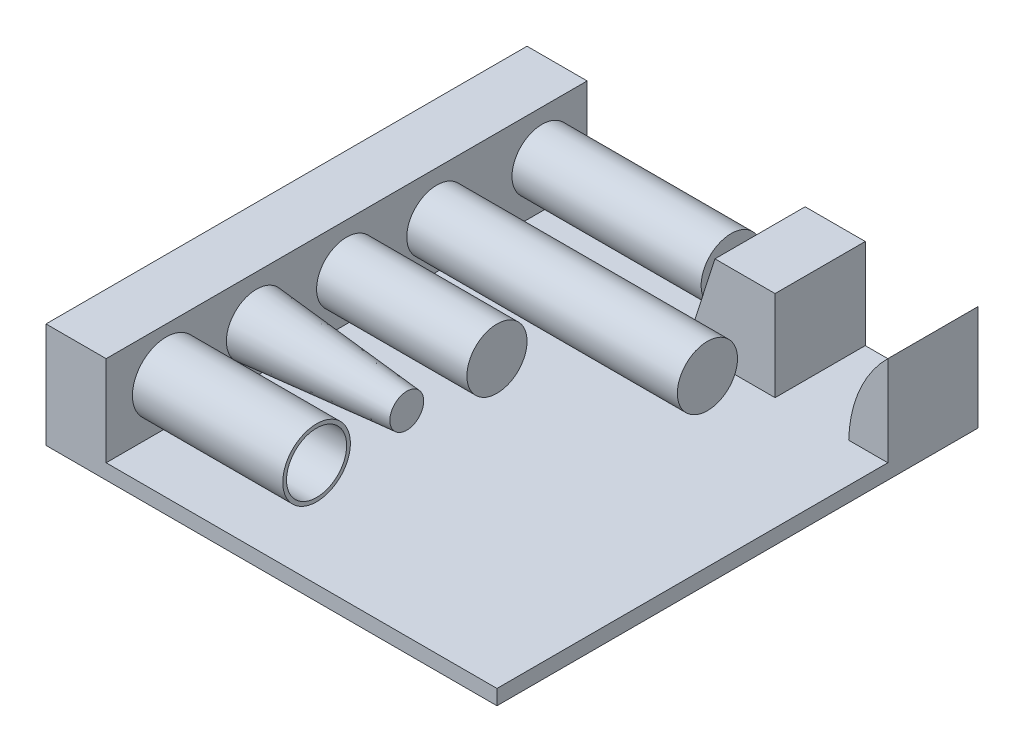
SolidWorks part; units mm, degrees
ref_plane "Front Plane" through (0, 0, 0) normal (0, 0, 1) x (1, 0, 0)
ref_plane "Top Plane" through (0, 0, 0) normal (0, 1, 0) x (1, 0, 0)
ref_plane "Right Plane" through (0, 0, 0) normal (1, 0, 0) x (0, 0, -1)
sketch "Sketch1" plane through (0, 0, 0) normal (0, 0, 1) x (1, 0, 0)
  line L0 (-300, 0) -> (300, 0)
  line L1 (55, 0) -> (-55, 0) construction
  line L2 (-300, 0) -> (-300, 140)
  line L3 (-300, 140) -> (-220, 140)
  line L4 (-220, 140) -> (-220, 20)
  line L5 (0, -55) -> (0, 55) construction
  line L6 (-220, 20) -> (300, 20)
  line L7 (300, 20) -> (300, 0)
  dimension "D1" = 600
  dimension "D2" = 80
  dimension "D3" = 300
  dimension "D4" = 220
  dimension "D5" = 20
  dimension "D6" = 140
extrude "Boss-Extrude1" add sketch "Sketch1" along normal blind 640
sketch "Sketch2" plane through (0, 0, 0) normal (0, 0, 1) x (1, 0, 0)
  line L0 (-220, 140) -> (323.1378, 140) construction
  line L1 (300, 20) -> (300, 140) construction
  line L6 (300, 20) -> (-220, 20) construction
  line L7 (300, 140) -> (300, 20)
  line L8 (300, 20) -> (247.9563, 20)
  line L9 (70, 140) -> (30, 15) construction
  line L11 (150, -14.017) -> (150, 140) construction
  line L12 (150, 140) -> (70, 140)
  line L13 (-220, 20) -> (-220, 140) construction
  line L14 (150, 140) -> (150, 20)
  line L15 (150, 20) -> (31.6, 20)
  line L16 (31.6, 20) -> (70, 140)
  arc A0 (300, 140) -> (247.9563, 20) centre (423.8522, 15) ccw
  point P8 (247.9563, 20)
  point P14 (150, 20)
  point P18 (31.6, 20)
  point P19 (150, 62.9915)
  dimension "D1" = 290
  dimension "D2" = 250
  dimension "D3" = 150
extrude "Boss-Extrude2" add sketch "Sketch2" along normal blind 120
sketch "One_Side" plane through (-220, 0, 0) normal (1, 0, 0) x (0, 0, -1)
  circle A0 centre (-60, 80) radius 40
ref_plane "Plane1" through (-60, 0, 0) normal (1, 0, 0) x (0, 0, -1)
sketch "Both_Sides" plane through (-60, 0, 0) normal (1, 0, 0) x (0, 0, -1)
  circle A0 centre (-200, 80) radius 40
sketch "Solid" plane through (-220, 0, 0) normal (1, 0, 0) x (0, 0, -1)
  circle A0 centre (-320, 80) radius 40
sketch "Thicken" plane through (-220, 0, 0) normal (1, 0, 0) x (0, 0, -1)
  circle A1 centre (-560, 80) radius 40
sketch "Draft" plane through (-220, 0, 0) normal (1, 0, 0) x (0, 0, -1)
  circle A0 centre (-440, 80) radius 40
extrude "Boss-Extrude3" add sketch "One_Side" along normal up to vertex (480.3305 mm away)
extrude "Boss-Extrude4" add sketch "Both_Sides" along normal blind 200 and the other way up to next
extrude "Boss-Extrude5" add sketch "Solid" along normal blind 200
extrude "Boss-Extrude6" add sketch "Draft" along normal blind 200 draft 5
extrude "Extrude-Thin1" add sketch "Thicken" along normal blind 200 thin
